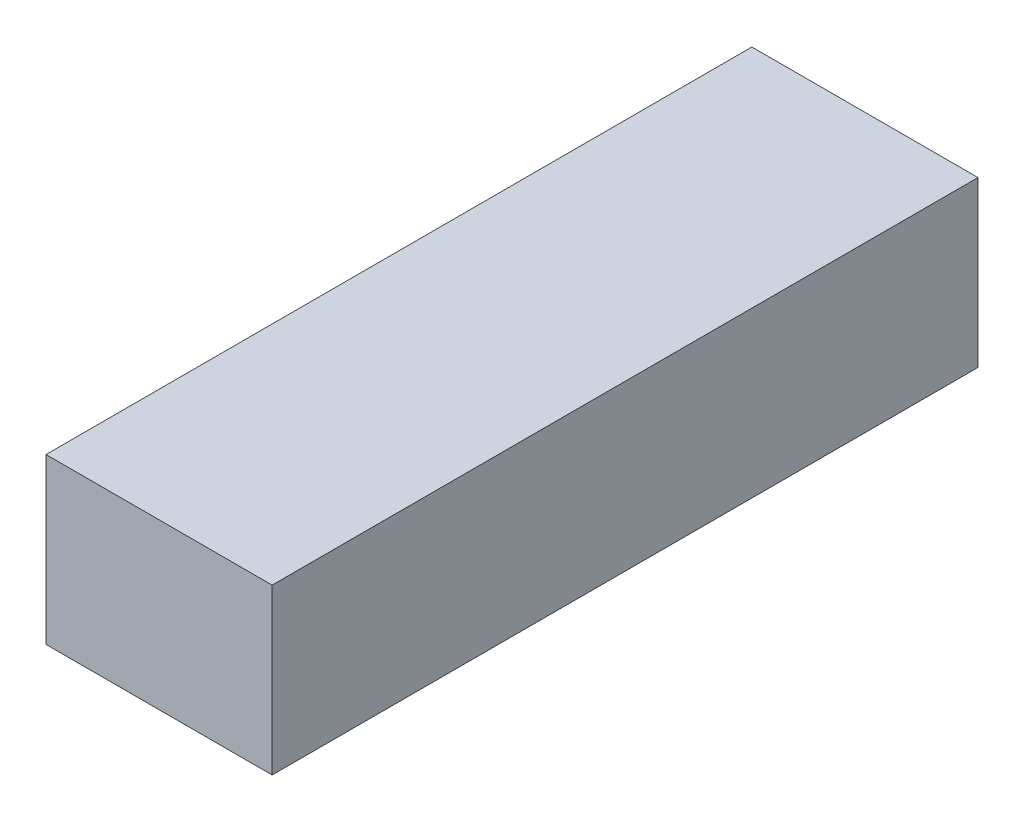
SolidWorks part; units mm, degrees
ref_plane "Front Plane" through (0, 0, 0) normal (0, 0, 1) x (1, 0, 0)
ref_plane "Top Plane" through (0, 0, 0) normal (0, 1, 0) x (1, 0, 0)
ref_plane "Right Plane" through (0, 0, 0) normal (1, 0, 0) x (0, 0, -1)
sketch "Sketch1" plane through (0, 0, 0) normal (0, 1, 0) x (1, 0, 0)
  line L1 (-16.5, -51.5) -> (16.5, -51.5)
  line L2 (-16.5, -51.5) -> (-16.5, 51.5)
  line L3 (-16.5, 51.5) -> (16.5, 51.5)
  line L4 (16.5, -51.5) -> (16.5, 51.5)
  line L5 (-16.5, -51.5) -> (16.5, 51.5) construction
  line L6 (-16.5, 51.5) -> (16.5, -51.5) construction
  point P0 (0, 0)
  dimension "D1" = 103
  dimension "D2" = 33
extrude "Boss-Extrude1" add sketch "Sketch1" along normal blind 24
ref_plane "Plane2" through (0, 0, 0) normal (1, 0, 0) x (0, 0, -1)
